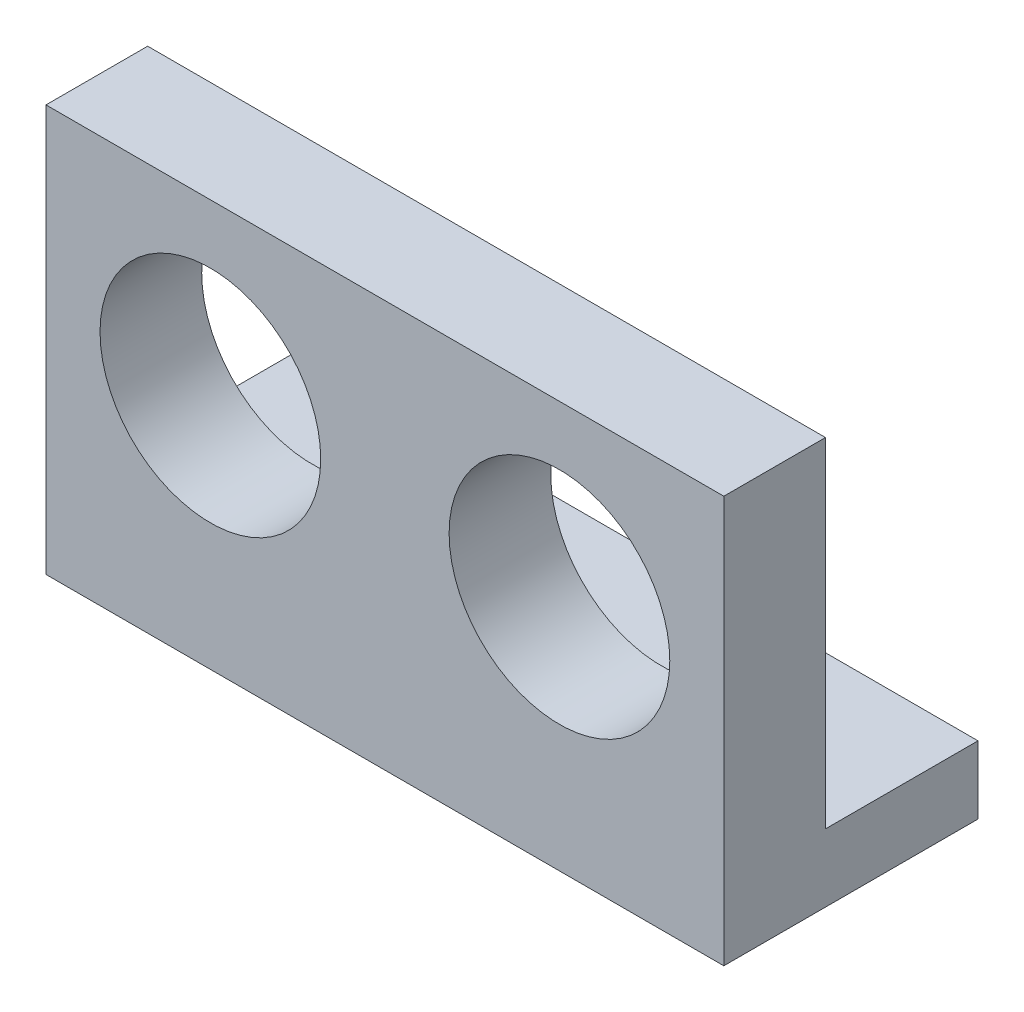
SolidWorks part; units mm, degrees
material "ABS"
ref_plane "Front Plane" through (0, 0, 0) normal (0, 0, 1) x (1, 0, 0)
ref_plane "Top Plane" through (0, 0, 0) normal (0, 1, 0) x (1, 0, 0)
ref_plane "Right Plane" through (0, 0, 0) normal (1, 0, 0) x (0, 0, -1)
sketch "Sketch11" plane through (0, 0, 0) normal (0, 0, 1) x (1, 0, 0)
  circle A10 centre (13.081, 12.7) radius 8.2697
  circle A12 centre (-13.081, 12.7) radius 8.2697
sketch "Sketch12" plane through (0, 0, 0) normal (0, 0, 1) x (1, 0, 0)
  line L1 (-25.4, 0) -> (25.4, 0)
  line L2 (-25.4, 0) -> (-25.4, 25.4)
  line L3 (-25.4, 25.4) -> (25.4, 25.4)
  line L4 (25.4, 0) -> (25.4, 25.4)
  circle A0 centre (13.081, 12.7) radius 8.2697 construction
  point P0 (0, 0)
  dimension "D1" = 12.7
  dimension "D2" = 50.8
  dimension "D3" = 25.4
extrude "Boss-Extrude1" add sketch "Sketch12" along normal blind 7.62
extrude "Cut-Extrude2" cut sketch "Sketch11" along normal through all contours A10 | A12
sketch "Sketch14" plane through (0, 0, 0) normal (0, -1, 0) x (-1, 0, 0)
  line L1 (-25.4, -7.62) -> (25.4, -7.62)
  line L2 (-25.4, -7.62) -> (-25.4, 11.43)
  line L3 (-25.4, 11.43) -> (25.4, 11.43)
  line L4 (25.4, -7.62) -> (25.4, 11.43)
  dimension "D1" = 19.05
extrude "Boss-Extrude2" add sketch "Sketch14" along normal blind 5.08
